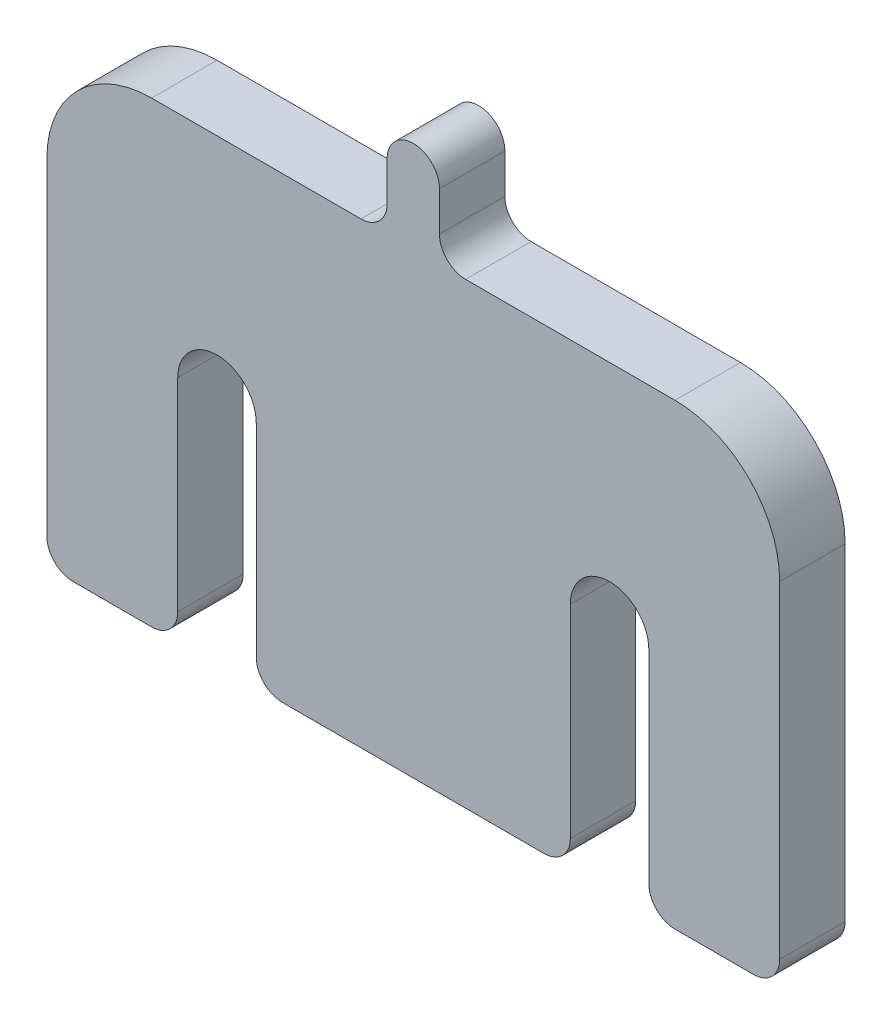
SolidWorks part; units mm, degrees
material "7075-O (SS)"
ref_plane "Płaszczyzna XY" through (0, 0, 0) normal (0, 0, 1) x (1, 0, 0)
ref_plane "Płaszczyzna XZ" through (0, 0, 0) normal (0, 1, 0) x (1, 0, 0)
ref_plane "Płaszczyzna YZ" through (0, 0, 0) normal (1, 0, 0) x (0, 0, -1)
sketch "Szkic1" plane through (0, 0, 0) normal (0, 0, 1) x (1, 0, 0)
  line L0 (15, 0) -> (-15, 0) construction
  line L1 (18, 0) -> (18, -17.5)
  line L2 (28, -17.5) -> (-28, -17.5)
  line L3 (28, -17.5) -> (28, 17.5)
  line L4 (28, 17.5) -> (-28, 17.5)
  line L5 (-28, -17.5) -> (-28, 17.5)
  line L6 (28, -17.5) -> (-28, 17.5) construction
  line L7 (28, 17.5) -> (-28, -17.5) construction
  line L8 (12, 0) -> (12, -17.5)
  line L9 (-12, 0) -> (-12, -17.5)
  line L10 (-18, 0) -> (-18, -17.5)
  line L11 (2, 22.5) -> (2, 17.5)
  line L12 (-2, 22.5) -> (-2, 17.5)
  line L13 (0, 22.5) -> (0, 0) construction
  arc A0 (-12, 0) -> (-18, 0) centre (-15, 0) ccw
  arc A1 (18, 0) -> (12, 0) centre (15, 0) ccw
  circle A2 centre (0, 22.5) radius 2
  point P1 (0, 0)
  point P6 (0, 0)
  dimension "D1" = 30
  dimension "D2" = 6
  dimension "D3" = 35
  dimension "D5" = 4
  dimension "D6" = 5
  dimension "D4" = 56
extrude "Dodanie-wyciągnięcie1" add sketch "Szkic1" along normal blind 5 contours A1 L1 L2 L3 L4 L5 L10 A0 L9 L8 | A2 L12 L4 L11 | A2
fillet "Zaokrąglenie1" radius 2 8 edges at (-28, -17.5, 2.5) (28, -17.5, 2.5) (-18, -17.5, 2.5) (-12, -17.5, 2.5) (12, -17.5, 2.5) (18, -17.5, 2.5) (-2, 17.5, 2.5) (2, 17.5, 2.5)
fillet "Zaokrąglenie2" radius 8 2 edges at (-28, 17.5, 2.5) (28, 17.5, 2.5)
